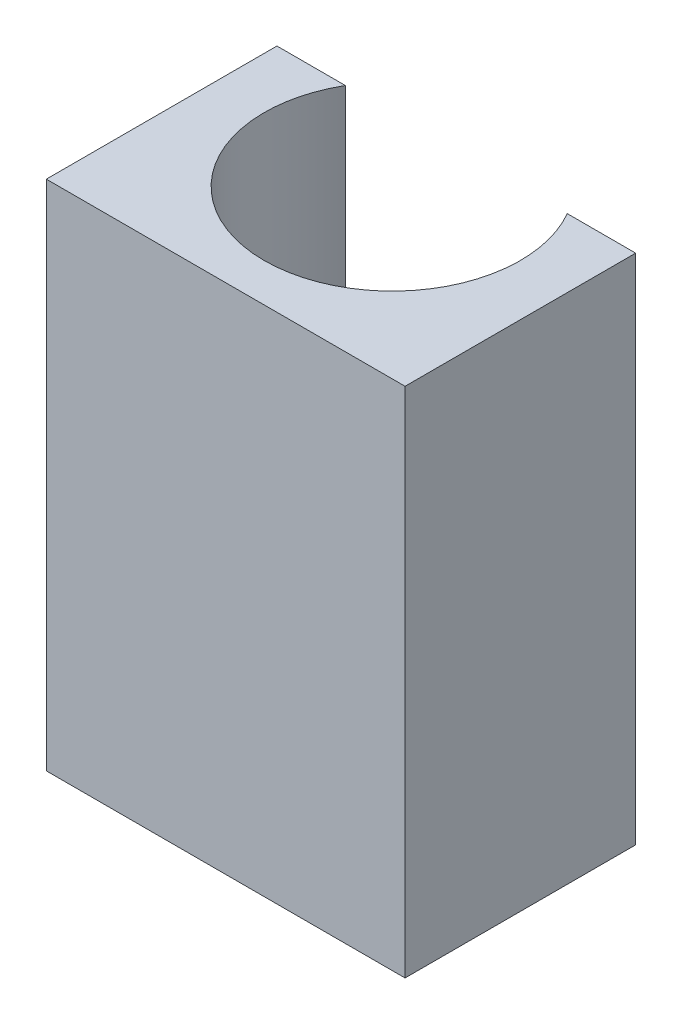
SolidWorks part; units mm, degrees
ref_plane "Front Plane" through (0, 0, 0) normal (0, 0, 1) x (1, 0, 0)
ref_plane "Top Plane" through (0, 0, 0) normal (0, 1, 0) x (1, 0, 0)
ref_plane "Right Plane" through (0, 0, 0) normal (1, 0, 0) x (0, 0, -1)
sketch "Sketch1" plane through (0, 0, 0) normal (0, 1, 0) x (1, 0, 0)
  line L0 (-4.3301, 4.5) -> (-7, 4.5)
  line L1 (7, -4.5) -> (-7, -4.5)
  line L2 (7, -4.5) -> (7, 4.5)
  line L3 (7, 4.5) -> (4.3301, 4.5)
  line L4 (-7, -4.5) -> (-7, 4.5)
  line L5 (7, -4.5) -> (-7, 4.5) construction
  line L6 (7, 4.5) -> (-7, -4.5) construction
  arc A0 (-4.3301, 4.5) -> (4.3301, 4.5) centre (0, 2) ccw
  point P0 (0, 0)
  point P8 (0, 1.9148)
  dimension "D2" = 10
  dimension "D4" = 6.5
  dimension "D1" = 14
  dimension "D3" = 9
extrude "Boss-Extrude1" add sketch "Sketch1" along normal blind 20
